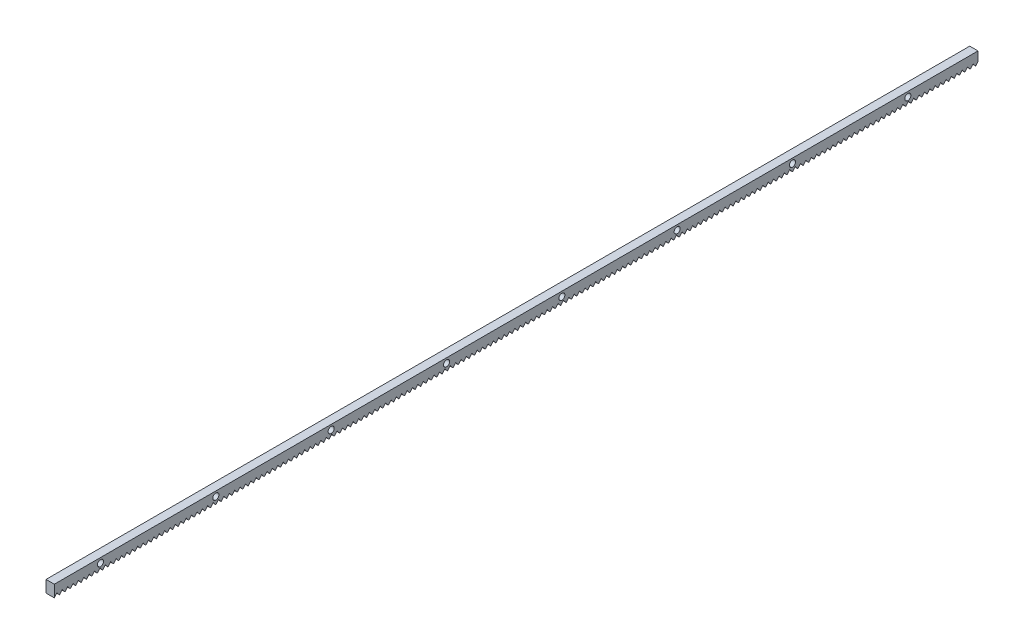
SolidWorks part; units mm, degrees
ref_plane "Front Plane" through (0, 0, 0) normal (0, 0, 1) x (1, 0, 0)
ref_plane "Top Plane" through (0, 0, 0) normal (0, 1, 0) x (1, 0, 0)
ref_plane "Right Plane" through (0, 0, 0) normal (1, 0, 0) x (0, 0, -1)
sketch "Sketch1" plane through (0, 0, 0) normal (0, 0, 1) x (1, 0, 0)
  line L1 (-20.9482, 4.4854) -> (-13.2482, 4.4854)
  line L2 (-20.9482, 4.4854) -> (-20.9482, -6.5146)
  line L3 (-20.9482, -6.5146) -> (-13.2482, -6.5146)
  line L4 (-13.2482, 4.4854) -> (-13.2482, -6.5146)
  dimension "D1" = 11
  dimension "D2" = 7.7
extrude "Boss-Extrude1" add sketch "Sketch1" along normal blind 857
sketch "Sketch2" plane through (-13.2482, 0, 0) normal (1, 0, 0) x (0, 0, -1)
  circle A0 centre (-814.1079, 0) radius 2.8382
extrude "Cut-Extrude1" cut sketch "Sketch2" against normal blind 900
pattern_linear "LPattern1" count 10 spacing 107 along (0, 0, -1) of "Cut-Extrude1"
sketch "Sketch3" plane through (-13.2482, 0, 0) normal (1, 0, 0) x (0, 0, -1)
  line L0 (-857.1094, -6.6301) -> (-854.6094, -3.5904)
  line L2 (-854.6094, -3.5904) -> (-852.1094, -6.6301)
  line L3 (-857.1094, -6.6301) -> (-852.1094, -6.6301)
  point P2 (-854.6094, -3.5904)
  point P4 (0, 0)
  point P6 (0, 0)
  dimension "D1" = 5
  dimension "D2" = 2.5
extrude "Cut-Extrude2" cut sketch "Sketch3" against normal blind 900
pattern_linear "LPattern2" count 200 spacing 5 along (0, 0, -1) of "Cut-Extrude2"
